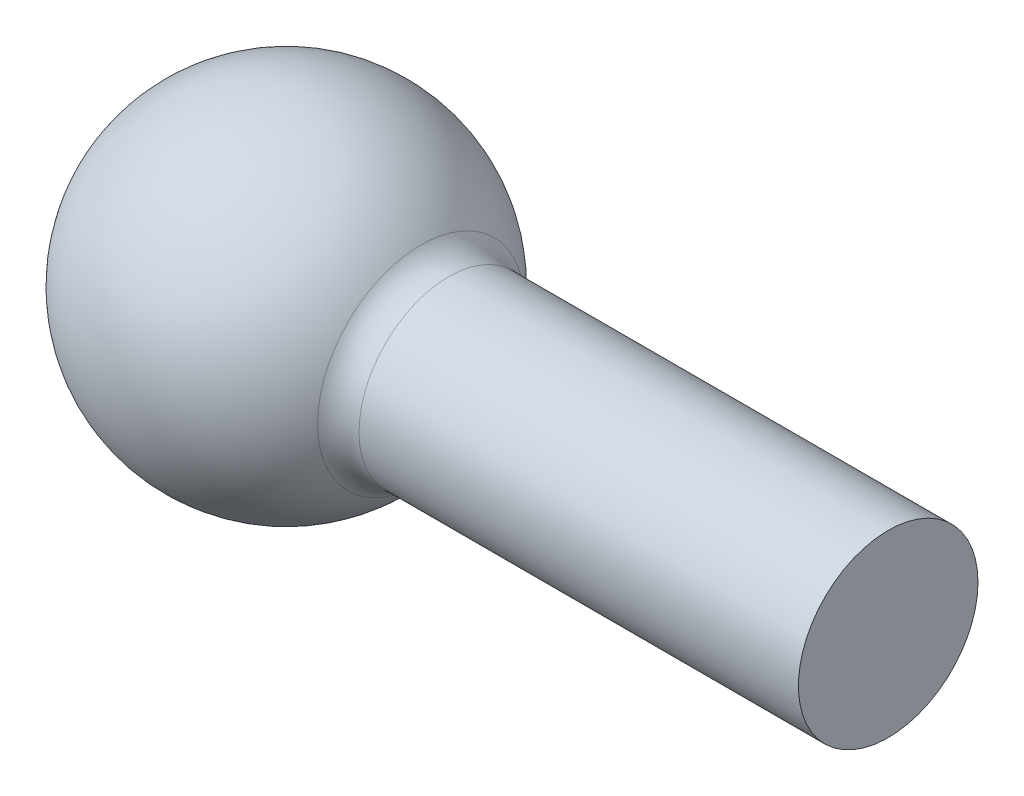
SolidWorks part; units mm, degrees
ref_plane "Front Plane" through (0, 0, 0) normal (0, 0, 1) x (1, 0, 0)
ref_plane "Top Plane" through (0, 0, 0) normal (0, 1, 0) x (1, 0, 0)
ref_plane "Right Plane" through (0, 0, 0) normal (1, 0, 0) x (0, 0, -1)
sketch "Sketch1" plane through (0, 0, 0) normal (0, 1, 0) x (1, 0, 0)
  line L3 (-4.7939, 25) -> (60.7061, 25)
  line L7 (60.7061, 12.15) -> (-49.7544, 12.15)
  line L12 (60.7061, 25) -> (60.7061, 12.15)
  arc A0 (-4.7939, 25) -> (-49.7544, 12.15) centre (-25.4379, 12.15) ccw
  dimension "D1" = 65.5
  dimension "D3" = 12.85
revolve "Revolve2" add sketch "Sketch1" angle 360 about L7
fillet "Fillet3" radius 5 1 edges at (-4.7939, 0, -25)
